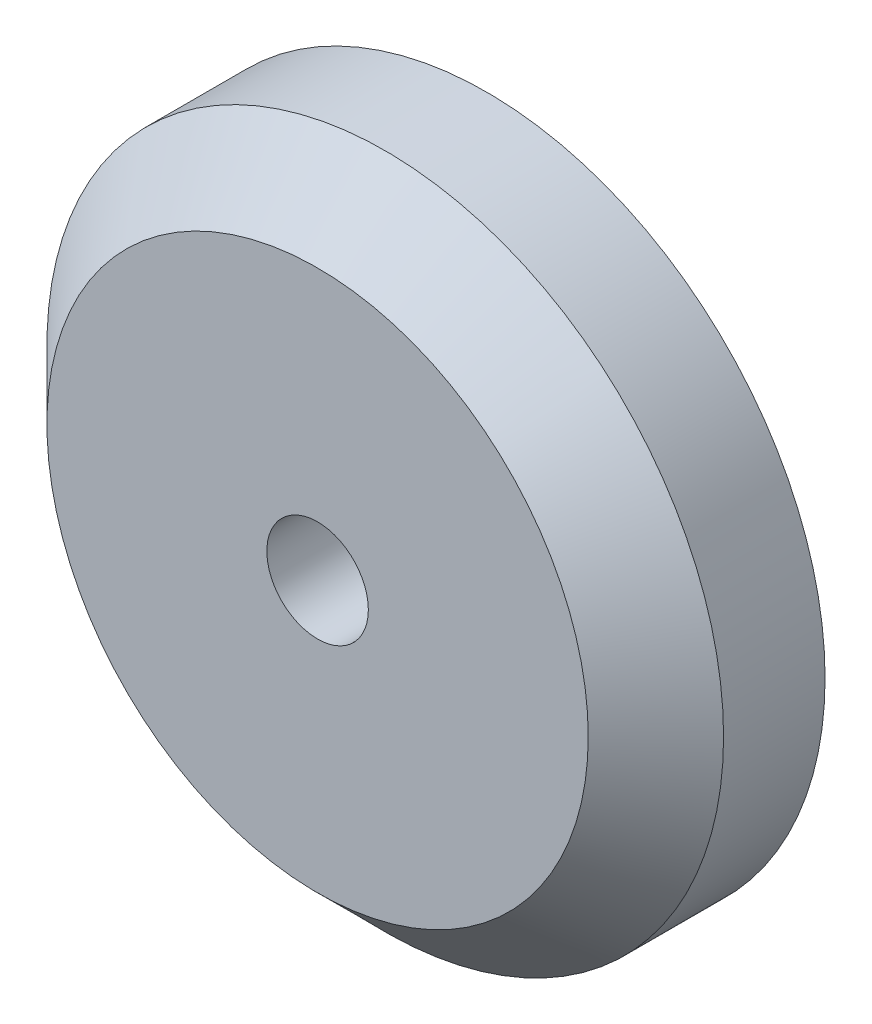
SolidWorks part; units mm, degrees
ref_plane "Front Plane" through (0, 0, 0) normal (0, 0, 1) x (1, 0, 0)
ref_plane "Top Plane" through (0, 0, 0) normal (0, 1, 0) x (1, 0, 0)
ref_plane "Right Plane" through (0, 0, 0) normal (1, 0, 0) x (0, 0, -1)
sketch "Sketch1" plane through (0, 0, 0) normal (0, 0, 1) x (1, 0, 0)
  circle A0 centre (0, 0) radius 10
  dimension "D1" = 20
extrude "Boss-Extrude1" add sketch "Sketch1" along normal blind 5
chamfer "Chamfer1" distance 2 angle 45 1 edges at (10, 0, 5)
sketch "Sketch2" plane through (0, 0, 5) normal (0, 0, 1) x (1, 0, 0)
  circle A0 centre (0, 0) radius 1.5
  dimension "D1" = 3
extrude "Cut-Extrude1" cut sketch "Sketch2" against normal blind 5
